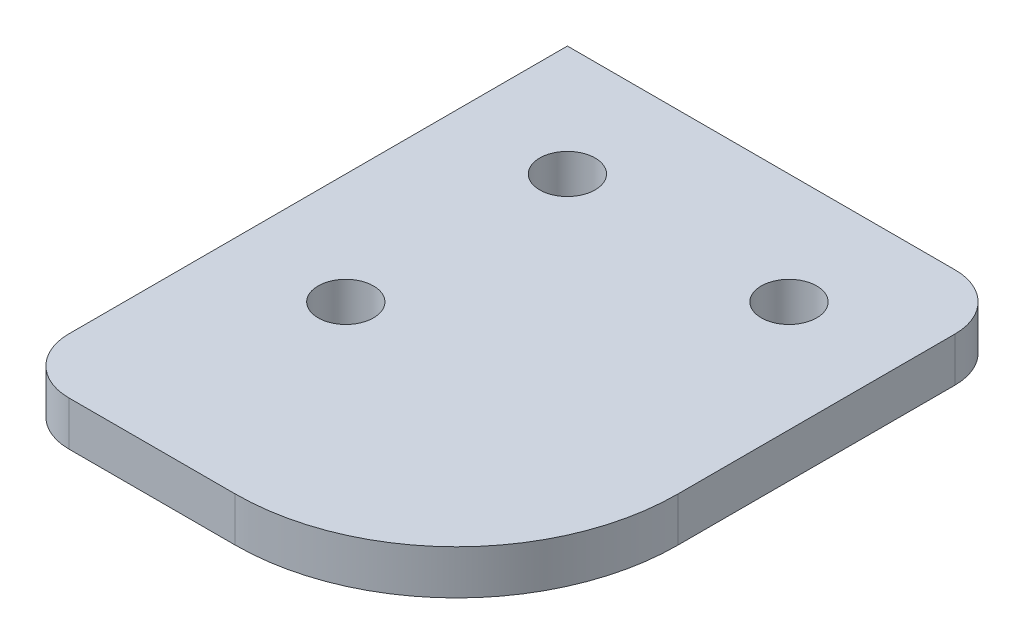
SolidWorks part; units mm, degrees
ref_plane "Front" through (0, 0, 0) normal (0, 0, 1) x (1, 0, 0)
ref_plane "Top" through (0, 0, 0) normal (0, 1, 0) x (1, 0, 0)
ref_plane "Right" through (0, 0, 0) normal (1, 0, 0) x (0, 0, -1)
sketch "Sketch1" plane through (0, 0, 0) normal (0, 1, 0) x (1, 0, 0)
  line L0 (0, 14.2138) -> (0, -4.1016) construction
  line L1 (-20, 20) -> (20, 20)
  line L2 (-20, 20) -> (-20, -30)
  line L4 (20, 20) -> (20, -10)
  line L5 (-20, -30) -> (0, -30)
  line L6 (-17.0016, 0) -> (16.742, 0) construction
  circle A0 centre (-10, 10) radius 2.5
  circle A3 centre (10, 10) radius 2.5
  arc A4 (20, -10) -> (0, -30) centre (0, -10) cw
  circle A5 centre (-10, -10) radius 2.5
  point P0 (0, 0)
  dimension "D2" = 10
  dimension "D1" = 40
  dimension "D3" = 50
  dimension "D4" = 30
extrude "Boss-Extrude1" add sketch "Sketch1" along normal blind 4
fillet "Fillet1" radius 5 2 edges at (20, 2, -20) (-20, 2, 30)
